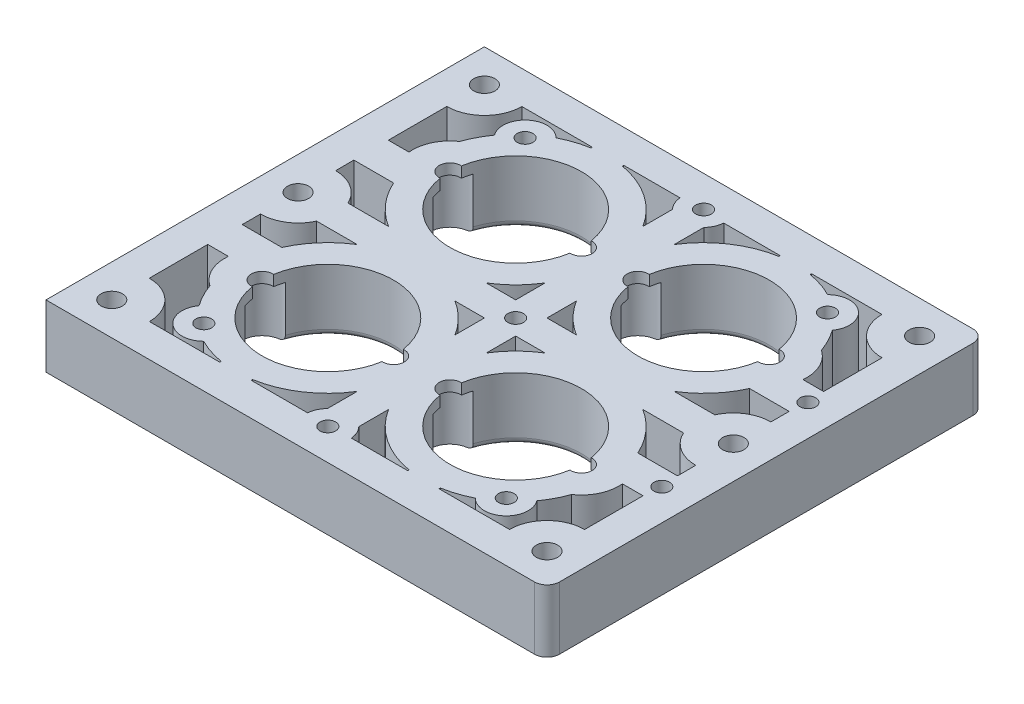
SolidWorks part; units mm, degrees
ref_plane "Front Plane" through (0, 0, 0) normal (0, 0, 1) x (1, 0, 0)
ref_plane "Top Plane" through (0, 0, 0) normal (0, 1, 0) x (1, 0, 0)
ref_plane "Right Plane" through (0, 0, 0) normal (1, 0, 0) x (0, 0, -1)
sketch "Sketch1" plane through (0, 0, 0) normal (0, 1, 0) x (1, 0, 0)
  line L1 (-42.6313, 37.6028) -> (37.3687, 37.6028)
  line L2 (-42.6313, 37.6028) -> (-42.6313, -32.3972)
  line L3 (-42.6313, -32.3972) -> (37.3687, -32.3972)
  line L4 (37.3687, 37.6028) -> (37.3687, -32.3972)
  dimension "D1" = 80
  dimension "D2" = 70
extrude "Boss-Extrude1" add sketch "Sketch1" along normal blind 10
sketch "Sketch3" plane through (0, 10, 0) normal (0, 1, 0) x (-1, 0, 0)
  line L0 (-37.3687, -37.6028) -> (42.6313, -37.6028) construction
  line L1 (42.6313, -37.6028) -> (42.6313, 32.3972) construction
  line L2 (-37.3687, 32.3972) -> (-37.3687, -37.6028) construction
  line L3 (42.6313, 32.3972) -> (-37.3687, 32.3972) construction
  circle A0 centre (17.6313, -17.6028) radius 10.5
  circle A1 centre (-12.3687, -17.6028) radius 10.5
  circle A2 centre (17.6313, 12.3972) radius 10.5
  circle A3 centre (-12.3687, 12.3972) radius 10.5
  dimension "D1" = 21
  dimension "D2" = 20
  dimension "D4" = 21
  dimension "D6" = 21
  dimension "D7" = 20
  dimension "D8" = 21
  dimension "D3" = 25
  dimension "D5" = 25
  dimension "D9" = 25
  dimension "D10" = 20
  dimension "D11" = 25
  dimension "D12" = 20
extrude "Cut-Extrude2" cut sketch "Sketch3" against normal up to next
sketch "Sketch4" plane through (0, 10, 0) normal (0, 1, 0) x (1, 0, 0)
  line L0 (-42.6313, -32.3972) -> (37.3687, -32.3972) construction
  line L1 (-42.6313, 37.6028) -> (-42.6313, -32.3972) construction
  line L2 (37.3687, -32.3972) -> (37.3687, 37.6028) construction
  line L3 (37.3687, 37.6028) -> (-42.6313, 37.6028) construction
  point P0 (-26.7813, -23.0472)
  point P5 (21.5187, -23.0472)
  point P8 (-26.7813, 28.2528)
  point P9 (21.5187, 28.2528)
  dimension "D1" = 9.35
  dimension "D2" = 15.85
  dimension "D3" = 15.85
  dimension "D4" = 9.35
  dimension "D5" = 9.35
hole_wizard "M3x0.5 Tapped Hole1" positions "3DSketch1" profile "Sketch5" tap size "M3x0.5" standard "Ansi Metric" end condition up to next
sketch3d "3DSketch1"
  point P0 (-26.7813, 10, 23.0472)
  point P3 (-26.7813, 10, -28.2528)
  point P6 (21.5187, 10, -28.2528)
  point P9 (21.5187, 10, 23.0472)
sketch "Sketch5" plane through (-26.7813, 10, 23.0472) normal (1, 0, 0) x (0, 0, 1)
  line L0 (0, 0) -> (0, 10)
  line L1 (0, 10) -> (1.25, 10)
  line L2 (1.25, 10) -> (1.25, 0)
  line L5 (1.25, 0) -> (0, 0)
  line L11 (0, -6.35) -> (0, 107.95) construction
  dimension "Thread Major Dia." = 2.5
  dimension "Thru Tap Drill Depth" = 10
sketch "Sketch10" plane through (0, 0, 0) normal (0, -1, 0) x (1, 0, 0)
  line L0 (-42.6313, -37.6028) -> (-42.6313, 32.3972) construction
  line L1 (-42.6313, 32.3972) -> (37.3687, 32.3972) construction
  line L2 (37.3687, -37.6028) -> (-42.6313, -37.6028) construction
  line L3 (37.3687, 32.3972) -> (37.3687, -37.6028) construction
  point P0 (-37.3813, 27.1472)
  point P1 (-37.3813, -2.6028)
  point P2 (-37.3813, -32.3528)
  point P11 (32.1187, 27.1472)
  point P12 (32.1187, -2.6028)
  point P13 (32.1187, -32.3528)
  dimension "D1" = 5.25
  dimension "D2" = 5.25
  dimension "D3" = 5.25
  dimension "D4" = 35
  dimension "D5" = 5.25
hole_wizard "CBORE for M3 SHCS1" positions "3DSketch3" profile "Sketch11" counterbore size "M3" standard "Ansi Metric" end condition up to next
sketch3d "3DSketch3"
  point P0 (-37.3813, 0, 27.1472)
  point P3 (-37.3813, 0, -2.6028)
  point P6 (-37.3813, 0, -32.3528)
  point P9 (32.1187, 0, 27.1472)
  point P12 (32.1187, 0, -2.6028)
  point P15 (32.1187, 0, -32.3528)
sketch "Sketch11" plane through (-37.3813, 0, 27.1472) normal (1, 0, 0) x (0, 0, -1)
  line L0 (0, 0) -> (0, 10)
  line L1 (0, 10) -> (1.7, 10)
  line L3 (1.7, 10) -> (1.7, 6)
  line L4 (1.7, 6) -> (3.25, 6)
  line L5 (3.25, 6) -> (3.25, 0)
  line L7 (3.25, 0) -> (0, 0)
  line L11 (0, -6.35) -> (0, 107.95) construction
  dimension "Thru Hole Dia." = 3.4
  dimension "Thru Hole Depth" = 10
  dimension "C'Bore Dia." = 6.5
  dimension "C'Bore Depth" = 6
fillet "Fillet3" radius 1 4 edges at (12.3687, 0, 22.8972) (12.3687, 0, -7.1028) (-17.6313, 0, 22.8972) (-17.6313, 0, -7.1028)
sketch "Sketch12" plane through (-42.6313, 0, 0) normal (-1, 0, 0) x (0, 0, 1)
  line L0 (-37.6028, 0) -> (32.3972, 0) construction
  line L1 (32.3972, 10) -> (32.3972, 0) construction
  line L2 (-37.6028, 10) -> (-37.6028, 0) construction
  line L3 (-37.6028, 10) -> (32.3972, 10) construction
  point P0 (9.0639, 5)
  point P1 (-14.2694, 5)
  dimension "D1" = 5
  dimension "D2" = 23.3333
  dimension "D3" = 23.3333
  dimension "D4" = 5
hole_wizard "Tap Drill for M3x0.5 Tap1" positions "3DSketch4" profile "Sketch14" hole size "M3x0.5" standard "Ansi Metric"
sketch3d "3DSketch4"
  point P0 (-42.6313, 5, 9.0639)
  point P3 (-42.6313, 5, -14.2694)
sketch "Sketch14" plane through (-42.6313, 5, 9.0639) normal (0, 1, 0) x (0, 0, 1)
  line L0 (0, 0) -> (0, 10.7511)
  line L1 (0, 10.7511) -> (1.25, 10)
  line L2 (1.25, 10) -> (1.25, 0)
  line L5 (1.25, 0) -> (0, 0)
  line L10 (0, 10.7511) -> (-1.25, 10) construction
  line L11 (0, -6.35) -> (0, 107.95) construction
  dimension "Hole Dia." = 2.5
  dimension "Hole Depth" = 10
  dimension "Drill Angle" = 118
fillet "Fillet4" radius 2 2 edges at (37.3687, 5, -37.6028) (37.3687, 5, 32.3972)
sketch "Sketch15" plane through (0, 0, 0) normal (0, -1, 0) x (1, 0, 0)
  line L0 (-29.1313, 12.3972) -> (23.8687, 12.3972) construction
  line L1 (-29.1313, -17.6028) -> (23.8687, -17.6028) construction
  circle A0 centre (-17.6313, 12.3972) radius 11.5 construction
  circle A1 centre (12.3687, 12.3972) radius 11.5 construction
  circle A2 centre (-17.6313, -17.6028) radius 11.5 construction
  circle A3 centre (12.3687, -17.6028) radius 11.5 construction
  circle A4 centre (-17.6313, 12.3972) radius 10.5 construction
  circle A5 centre (12.3687, 12.3972) radius 10.5 construction
  circle A6 centre (-17.6313, -17.6028) radius 10.5 construction
  circle A7 centre (12.3687, -17.6028) radius 10.5 construction
  point P14 (-17.6313, 12.3972)
  point P15 (-28.1313, 12.3972)
  point P19 (-7.1313, 12.3972)
  point P20 (1.8687, 12.3972)
  point P21 (22.8687, 12.3972)
  point P24 (-28.1313, -17.6028)
  point P25 (-7.1313, -17.6028)
  point P26 (1.8687, -17.6028)
  point P27 (22.8687, -17.6028)
hole_wizard "CBORE for M3 SHCS2" positions "3DSketch5" profile "Sketch16" counterbore size "M3" standard "Ansi Metric" end condition through all
sketch3d "3DSketch5"
  point P0 (-28.1313, 0, 12.3972)
  point P3 (1.8687, 0, 12.3972)
  point P6 (-7.1313, 0, 12.3972)
  point P9 (22.8687, 0, 12.3972)
  point P12 (-28.1313, 0, -17.6028)
  point P15 (-7.1313, 0, -17.6028)
  point P18 (1.8687, 0, -17.6028)
  point P21 (22.8687, 0, -17.6028)
sketch "Sketch16" plane through (-28.1313, 0, 12.3972) normal (1, 0, 0) x (0, 0, -1)
  line L0 (0, 0) -> (0, 10)
  line L1 (0, 10) -> (1.7, 10)
  line L3 (1.7, 10) -> (1.7, 8.3)
  line L4 (1.7, 8.3) -> (3.25, 8.3)
  line L5 (3.25, 8.3) -> (3.25, 0)
  line L7 (3.25, 0) -> (0, 0)
  line L11 (0, -6.35) -> (0, 107.95) construction
  dimension "Thru Hole Dia." = 3.4
  dimension "Thru Hole Depth" = 10
  dimension "C'Bore Dia." = 6.5
  dimension "C'Bore Depth" = 8.3
sketch "Sketch18" plane through (0, 0, 0) normal (0, -1, 0) x (1, 0, 0)
  line L0 (37.3687, 30.3972) -> (37.3687, -35.6028) construction
  line L1 (-42.6313, 32.3972) -> (35.3687, 32.3972) construction
  line L2 (35.3687, -37.6028) -> (-42.6313, -37.6028) construction
  point P0 (32.3687, 9.0639)
  point P1 (32.3687, -14.2694)
  point P2 (-2.6313, -2.6028)
  point P3 (-2.6313, -32.6028)
  point P10 (-2.6313, 27.3972)
  dimension "D1" = 5
  dimension "D2" = 5
  dimension "D3" = 23.3333
  dimension "D4" = 23.3333
  dimension "D5" = 40
  dimension "D6" = 35
  dimension "D7" = 5
  dimension "D8" = 5
  dimension "D9" = 40
  dimension "D10" = 40
hole_wizard "Tap Drill for M3x0.5 Tap2" positions "3DSketch6" profile "Sketch20" hole size "M3x0.5" standard "Ansi Metric" end condition up to next
sketch3d "3DSketch6"
  point P0 (-2.6313, 0, 27.3972)
  point P3 (-2.6313, 0, -2.6028)
  point P6 (-2.6313, 0, -32.6028)
  point P9 (32.3687, 0, -14.2694)
  point P12 (32.3687, 0, 9.0639)
sketch "Sketch20" plane through (-2.6313, 0, 27.3972) normal (1, 0, 0) x (0, 0, -1)
  line L0 (0, 0) -> (0, 10)
  line L1 (0, 10) -> (1.25, 10)
  line L2 (1.25, 10) -> (1.25, 0)
  line L5 (1.25, 0) -> (0, 0)
  line L11 (0, -6.35) -> (0, 107.95) construction
  dimension "Thru Hole Dia." = 2.5
  dimension "Thru Hole Depth" = 10
sketch "Sketch21" plane through (0, 0, 0) normal (0, -1, 0) x (1, 0, 0)
  line L0 (-31.3813, 27.1335) -> (-20.1313, 27.1335)
  line L1 (-34.0917, 11.8139) -> (-37.3871, 11.8139)
  line L2 (-37.3871, 21.1472) -> (-37.3871, 11.8139)
  line L3 (-32.6313, 10.3139) -> (-42.6313, 10.3139) construction
  line L4 (-31.0533, 6.3139) -> (-37.3871, 6.3139)
  line L5 (-42.6313, 7.8139) -> (-32.6313, 7.8139) construction
  line L6 (-37.3871, 6.3139) -> (-37.3813, 3.3972)
  line L7 (-37.3813, -2.6028) -> (32.1187, -2.6028) construction
  line L8 (-2.6313, 27.3972) -> (-2.6313, -32.6028) construction
  line L9 (-9.8268, -0.1028) -> (-5.1313, -0.1028)
  line L10 (-15.1313, 27.1335) -> (-6.1213, 27.1335)
  line L11 (-5.1313, 4.5928) -> (-5.1313, -0.1028)
  line L12 (-31.9269, -0.1028) -> (-25.4357, -0.1028)
  line L13 (-5.1313, 24.9477) -> (-5.1313, 20.2017)
  line L14 (-15.1313, 27.1335) -> (-15.1313, 26.9199)
  line L15 (-20.1313, 26.9199) -> (-20.1313, 27.1335)
  line L16 (14.8687, 26.9199) -> (14.8687, 27.1335)
  line L17 (9.8687, 27.1335) -> (9.8687, 26.9199)
  line L18 (-0.1313, 24.9477) -> (-0.1313, 20.2017)
  line L19 (26.6644, -0.1028) -> (20.1732, -0.1028)
  line L20 (-0.1313, 4.5928) -> (-0.1313, -0.1028)
  line L21 (9.8687, 27.1335) -> (0.8588, 27.1335)
  line L22 (4.5643, -0.1028) -> (-0.1313, -0.1028)
  line L23 (32.1246, 6.3139) -> (32.1187, 3.3972)
  line L24 (25.7908, 6.3139) -> (32.1246, 6.3139)
  line L25 (32.1246, 21.1472) -> (32.1246, 11.8139)
  line L26 (28.8292, 11.8139) -> (32.1246, 11.8139)
  line L27 (26.1188, 27.1335) -> (14.8687, 27.1335)
  line L28 (26.1188, -32.3391) -> (14.8687, -32.3391)
  line L29 (28.8292, -17.0194) -> (32.1246, -17.0194)
  line L30 (32.1246, -26.3528) -> (32.1246, -17.0194)
  line L31 (25.7908, -11.5194) -> (32.1246, -11.5194)
  line L32 (32.1246, -11.5194) -> (32.1187, -8.6028)
  line L33 (4.5643, -5.1028) -> (-0.1313, -5.1028)
  line L34 (9.8687, -32.3391) -> (0.8588, -32.3391)
  line L35 (-0.1313, -9.7983) -> (-0.1313, -5.1028)
  line L36 (26.6644, -5.1028) -> (20.1732, -5.1028)
  line L37 (-0.1313, -30.1533) -> (-0.1313, -25.4072)
  line L38 (9.8687, -32.3391) -> (9.8687, -32.1255)
  line L39 (14.8687, -32.1255) -> (14.8687, -32.3391)
  line L40 (-20.1313, -32.1255) -> (-20.1313, -32.3391)
  line L41 (-15.1313, -32.3391) -> (-15.1313, -32.1255)
  line L42 (-5.1313, -30.1533) -> (-5.1313, -25.4072)
  line L43 (-31.9269, -5.1028) -> (-25.4357, -5.1028)
  line L44 (-5.1313, -9.7983) -> (-5.1313, -5.1028)
  line L45 (-15.1313, -32.3391) -> (-6.1213, -32.3391)
  line L46 (-9.8268, -5.1028) -> (-5.1313, -5.1028)
  line L47 (-37.3871, -11.5194) -> (-37.3813, -8.6028)
  line L48 (-31.0533, -11.5194) -> (-37.3871, -11.5194)
  line L49 (-37.3871, -26.3528) -> (-37.3871, -17.0194)
  line L50 (-34.0917, -17.0194) -> (-37.3871, -17.0194)
  line L51 (-31.3813, -32.3391) -> (-20.1313, -32.3391)
  arc A0 (-37.3871, 21.1472) -> (-31.3813, 27.1335) centre (-37.3813, 27.1472) ccw
  arc A1 (-34.0917, 11.8139) -> (-31.5142, 17.3392) centre (-28.1313, 12.3972) cw
  arc A2 (-29.6079, 20.9832) -> (-31.5142, 17.3392) centre (-17.6313, 12.3972) ccw
  arc A3 (-24.315, 25.5307) -> (-29.6079, 20.9832) centre (-26.7813, 23.0472) ccw
  arc A4 (-29.6079, 20.9832) -> (-31.5142, 17.3392) centre (-17.6313, 12.3972) ccw
  arc A5 (-31.9269, -0.1028) -> (-37.3813, 3.3972) centre (-37.3813, -2.6028) ccw
  arc A6 (-21.9346, 26.4912) -> (-20.1313, 26.9199) centre (-17.6313, 12.3972) cw
  arc A7 (-20.1313, 26.9199) -> (-24.315, 25.5307) centre (-17.6313, 12.3972) ccw
  arc A8 (-6.1213, 27.1335) -> (-5.1313, 24.9477) centre (-2.6313, 27.3972) ccw
  arc A9 (-9.8268, -0.1028) -> (-5.1313, 4.5928) centre (-17.6313, 12.3972) ccw
  arc A10 (-20.1313, 26.9199) -> (-24.315, 25.5307) centre (-17.6313, 12.3972) ccw
  arc A11 (-31.0533, 6.3139) -> (-25.4357, -0.1028) centre (-17.6313, 12.3972) ccw
  arc A12 (-29.6079, 20.9832) -> (-31.5142, 17.3392) centre (-17.6313, 12.3972) ccw
  arc A13 (-15.1313, 26.9199) -> (-5.1313, 20.2017) centre (-17.6313, 12.3972) cw
  arc A14 (14.8687, 26.9199) -> (19.0525, 25.5307) centre (12.3687, 12.3972) cw
  arc A15 (9.8687, 26.9199) -> (-0.1313, 20.2017) centre (12.3687, 12.3972) ccw
  arc A16 (24.3454, 20.9832) -> (26.2517, 17.3392) centre (12.3687, 12.3972) cw
  arc A17 (25.7908, 6.3139) -> (20.1732, -0.1028) centre (12.3687, 12.3972) cw
  arc A18 (14.8687, 26.9199) -> (19.0525, 25.5307) centre (12.3687, 12.3972) cw
  arc A19 (4.5643, -0.1028) -> (-0.1313, 4.5928) centre (12.3687, 12.3972) cw
  arc A20 (0.8588, 27.1335) -> (-0.1313, 24.9477) centre (-2.6313, 27.3972) cw
  arc A21 (14.8687, 26.9199) -> (19.0525, 25.5307) centre (12.3687, 12.3972) cw
  arc A22 (16.6721, 26.4912) -> (14.8687, 26.9199) centre (12.3687, 12.3972) ccw
  arc A23 (26.6644, -0.1028) -> (32.1187, 3.3972) centre (32.1187, -2.6028) cw
  arc A24 (24.3454, 20.9832) -> (26.2517, 17.3392) centre (12.3687, 12.3972) cw
  arc A25 (19.0525, 25.5307) -> (24.3454, 20.9832) centre (21.5187, 23.0472) cw
  arc A26 (24.3454, 20.9832) -> (26.2517, 17.3392) centre (12.3687, 12.3972) cw
  arc A27 (-20.1313, 26.9199) -> (-24.315, 25.5307) centre (-17.6313, 12.3972) ccw
  arc A28 (28.8292, 11.8139) -> (26.2517, 17.3392) centre (22.8687, 12.3972) ccw
  arc A29 (32.1246, 21.1472) -> (26.1188, 27.1335) centre (32.1187, 27.1472) cw
  arc A30 (32.1246, -26.3528) -> (26.1188, -32.3391) centre (32.1187, -32.3528) ccw
  arc A31 (28.8292, -17.0194) -> (26.2517, -22.5447) centre (22.8687, -17.6028) cw
  arc A32 (-20.1313, -32.1255) -> (-24.315, -30.7362) centre (-17.6313, -17.6028) cw
  arc A33 (24.3454, -26.1888) -> (26.2517, -22.5447) centre (12.3687, -17.6028) ccw
  arc A34 (19.0525, -30.7362) -> (24.3454, -26.1888) centre (21.5187, -28.2528) ccw
  arc A35 (24.3454, -26.1888) -> (26.2517, -22.5447) centre (12.3687, -17.6028) ccw
  arc A36 (26.6644, -5.1028) -> (32.1187, -8.6028) centre (32.1187, -2.6028) ccw
  arc A37 (16.6721, -31.6968) -> (14.8687, -32.1255) centre (12.3687, -17.6028) cw
  arc A38 (14.8687, -32.1255) -> (19.0525, -30.7362) centre (12.3687, -17.6028) ccw
  arc A39 (0.8588, -32.3391) -> (-0.1313, -30.1533) centre (-2.6313, -32.6028) ccw
  arc A40 (4.5643, -5.1028) -> (-0.1313, -9.7983) centre (12.3687, -17.6028) ccw
  arc A41 (14.8687, -32.1255) -> (19.0525, -30.7362) centre (12.3687, -17.6028) ccw
  arc A42 (25.7908, -11.5194) -> (20.1732, -5.1028) centre (12.3687, -17.6028) ccw
  arc A43 (24.3454, -26.1888) -> (26.2517, -22.5447) centre (12.3687, -17.6028) ccw
  arc A44 (9.8687, -32.1255) -> (-0.1313, -25.4072) centre (12.3687, -17.6028) cw
  arc A45 (14.8687, -32.1255) -> (19.0525, -30.7362) centre (12.3687, -17.6028) ccw
  arc A46 (-15.1313, -32.1255) -> (-5.1313, -25.4072) centre (-17.6313, -17.6028) ccw
  arc A47 (-29.6079, -26.1888) -> (-31.5142, -22.5447) centre (-17.6313, -17.6028) cw
  arc A48 (-31.0533, -11.5194) -> (-25.4357, -5.1028) centre (-17.6313, -17.6028) cw
  arc A49 (-20.1313, -32.1255) -> (-24.315, -30.7362) centre (-17.6313, -17.6028) cw
  arc A50 (-9.8268, -5.1028) -> (-5.1313, -9.7983) centre (-17.6313, -17.6028) cw
  arc A51 (-6.1213, -32.3391) -> (-5.1313, -30.1533) centre (-2.6313, -32.6028) cw
  arc A52 (-20.1313, -32.1255) -> (-24.315, -30.7362) centre (-17.6313, -17.6028) cw
  arc A53 (-21.9346, -31.6968) -> (-20.1313, -32.1255) centre (-17.6313, -17.6028) ccw
  arc A54 (-31.9269, -5.1028) -> (-37.3813, -8.6028) centre (-37.3813, -2.6028) cw
  arc A55 (-29.6079, -26.1888) -> (-31.5142, -22.5447) centre (-17.6313, -17.6028) cw
  arc A56 (-24.315, -30.7362) -> (-29.6079, -26.1888) centre (-26.7813, -28.2528) cw
  arc A57 (-29.6079, -26.1888) -> (-31.5142, -22.5447) centre (-17.6313, -17.6028) cw
  arc A58 (-34.0917, -17.0194) -> (-31.5142, -22.5447) centre (-28.1313, -17.6028) ccw
  arc A59 (-37.3871, -26.3528) -> (-31.3813, -32.3391) centre (-37.3813, -32.3528) cw
  dimension "D1" = 12
  dimension "D2" = 1.5
  dimension "D3" = 7
  dimension "D4" = 1.5
  dimension "D5" = 12
  dimension "D6" = 2.5
  dimension "D7" = 7
  dimension "D8" = 2.5
  dimension "D9" = 2.5
  dimension "D10" = 2.5
extrude "Cut-Extrude3" cut sketch "Sketch21" against normal blind 10 contours A7 A6 L15 L0 A0 L2 L1 A1 A2 A3 | L14 A13 L13 A8 L10 | A11 L4 L6 A5 L12 | L43 A54 L47 L48 A48 | L49 A59 L51 L40 A32 A52 A56 A47 A58 L50 | L45 A51 L42 A46 L41 | L46 A50 L44 | A9 L9 L11 | L22 A19 L20 | A40 L33 L35 | L38 A44 L37 A39 L34 | A38 A37 L39 L28 A30 L30 L29 A31 A33 A34 | A42 L31 L32 A36 L36 | L19 A23 L23 L24 A17 | L25 A29 L27 L16 A14 A21 A25 A16 A28 L26 | L21 A20 L18 A15 L17
